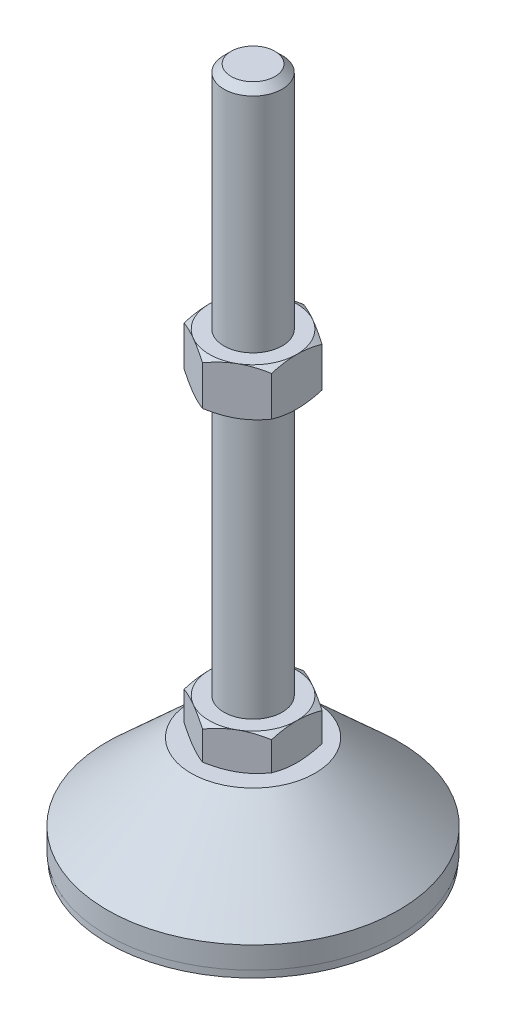
SolidWorks part; units mm, degrees
ref_plane "Спереди" through (0, 0, 0) normal (0, 0, 1) x (1, 0, 0)
ref_plane "Сверху" through (0, 0, 0) normal (0, 1, 0) x (1, 0, 0)
ref_plane "Справа" through (0, 0, 0) normal (1, 0, 0) x (0, 0, -1)
sketch "Эскиз1" plane through (0, 0, 0) normal (0, 0, 1) x (1, 0, 0)
  line L0 (0, 0) -> (-39.8, 0)
  line L1 (-39.8, 0) -> (-39.8, 2)
  line L2 (-39.8, 2) -> (-40, 2)
  line L3 (-40, 2) -> (-40, 8)
  line L4 (-40, 8) -> (-17, 29)
  line L5 (-17, 29) -> (-8, 29)
  line L12 (-8, 39) -> (-8, 187)
  line L13 (-8, 187) -> (-6, 189)
  line L14 (-6, 189) -> (0, 189)
  line L15 (0, 189) -> (0, 0) construction
  line L16 (-8, 29) -> (0, 29) construction
  line L17 (0, 0) -> (0, 189)
  line L18 (0, 0) -> (0, -7.9595) construction
  line L19 (-8, 39) -> (-8, 29)
  point P8 (-8, 113)
  point P23 (-12.5, 29)
  dimension "D1" = 16
  dimension "D2" = 29
  dimension "D3" = 10
  dimension "D4" = 80
  dimension "D5" = 8
  dimension "D6" = 2
  dimension "D7" = 45
  dimension "D8" = 34
  dimension "D9" = 2
  dimension "D10" = 150
  dimension "D11" = 6
  dimension "D12" = 0.2
revolve "Повернуть1" add sketch "Эскиз1" angle 360 about L17
sketch "Эскиз2" plane through (0, 29, 0) normal (0, 1, 0) x (1, 0, 0)
  line L1 (0, 13.8564) -> (-12, 6.9282)
  line L2 (-12, 6.9282) -> (-12, -6.9282)
  line L3 (-12, -6.9282) -> (0, -13.8564)
  line L4 (0, -13.8564) -> (12, -6.9282)
  line L5 (12, -6.9282) -> (12, 6.9282)
  line L6 (12, 6.9282) -> (0, 13.8564)
  circle A0 centre (0, 0) radius 12 construction
  dimension "D1" = 24
extrude "Бобышка-Вытянуть1" add sketch "Эскиз2" along normal up to vertex (10 mm away) up to point (-8, 39, 0)
ref_plane "Плоскость1" through (0, 113, 0) normal (0, 1, 0) x (1, 0, 0)
sketch "Эскиз3" plane through (0, 113, 0) normal (0, 1, 0) x (1, 0, 0)
  line L6 (12, 6.9282) -> (0, 13.8564)
  line L7 (0, 13.8564) -> (-12, 6.9282)
  line L8 (-12, 6.9282) -> (-12, -6.9282)
  line L9 (-12, -6.9282) -> (0, -13.8564)
  line L10 (0, -13.8564) -> (12, -6.9282)
  line L11 (12, -6.9282) -> (12, 6.9282)
  line L12 (12, 6.9282) -> (0, 13.8564)
  line L13 (0, 13.8564) -> (-12, 6.9282)
  line L14 (-12, 6.9282) -> (-12, -6.9282)
  line L15 (-12, -6.9282) -> (0, -13.8564)
  line L16 (0, -13.8564) -> (12, -6.9282)
  line L17 (12, -6.9282) -> (12, 6.9282)
  dimension "D1" = 0
extrude "Бобышка-Вытянуть2" add sketch "Эскиз3" along normal blind 13
sketch "Эскиз4" plane through (0, 0, 0) normal (0, 0, 1) x (1, 0, 0)
  line L0 (-12, 126) -> (-23.2583, 119.5)
  line L1 (-23.2583, 119.5) -> (-23.2583, 126)
  line L2 (-23.2583, 126) -> (-12, 126)
  line L3 (-23.2583, 119.5) -> (-12, 113)
  line L4 (50, 113) -> (-50, 113) construction
  line L5 (-12, 113) -> (-23.2583, 113)
  line L6 (-23.2583, 113) -> (-23.2583, 119.5)
  line L7 (-12, 126) -> (-12, 113) construction
  line L8 (-12, 39) -> (-20.6603, 39)
  line L9 (-20.6603, 39) -> (-20.6603, 34)
  line L10 (-20.6603, 34) -> (-12, 39)
  line L11 (-12, 29) -> (-20.6603, 34)
  line L12 (-20.6603, 34) -> (-20.6603, 29)
  line L13 (-20.6603, 29) -> (-12, 29)
  line L14 (0, 189) -> (0, 96.3793) construction
  dimension "D1" = 30
  dimension "D2" = 30
revolve "Вырез-Повернуть2" cut sketch "Эскиз4" angle 360 about L14
